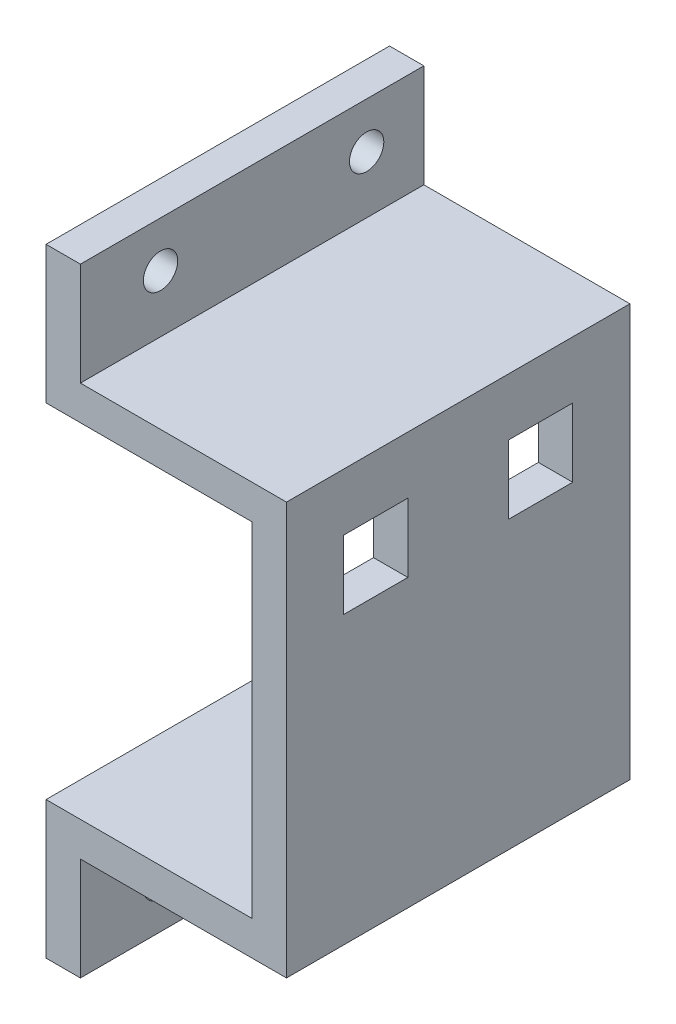
SolidWorks part; units mm, degrees
ref_plane "Front" through (0, 0, 0) normal (0, 0, 1) x (1, 0, 0)
ref_plane "Top" through (0, 0, 0) normal (0, 1, 0) x (1, 0, 0)
ref_plane "Right" through (0, 0, 0) normal (1, 0, 0) x (0, 0, -1)
sketch "草图1" plane through (0, 0, 0) normal (0, 0, 1) x (1, 0, 0)
  line L0 (0, 0) -> (18, 0)
  line L1 (18, 0) -> (18, -30)
  line L2 (18, -30) -> (0, -30)
  line L3 (0, -30) -> (0, -42)
  line L4 (0, 0) -> (0, 12)
  line L5 (3, 3) -> (3, 12)
  line L6 (3, 3) -> (21, 3)
  line L7 (21, 3) -> (21, -33)
  line L8 (21, -33) -> (3, -33)
  line L9 (3, -33) -> (3, -42)
  line L10 (0, 12) -> (3, 12)
  line L11 (3, -42) -> (0, -42)
  dimension "D1" = 12
  dimension "D2" = 30
  dimension "D3" = 18
  dimension "D4" = 3
extrude "凸台-拉伸1" add sketch "草图1" along normal mid plane 30
sketch "草图2" plane through (21, 0, 0) normal (1, 0, 0) x (0, 0, -1)
  line L0 (-15, -33) -> (-15, 3) construction
  line L1 (-10, -8) -> (-4.4, -8)
  line L2 (-10, -8) -> (-10, -2)
  line L3 (-10, -2) -> (-4.4, -2)
  line L4 (-4.4, -8) -> (-4.4, -2)
  line L5 (-10, -8) -> (-4.4, -2) construction
  line L6 (-10, -2) -> (-4.4, -8) construction
  line L7 (-15, 3) -> (15, 3) construction
  point P0 (-7.2, -5)
  dimension "D1" = 5.6
  dimension "D2" = 6
  dimension "D3" = 5
  dimension "D4" = 8
extrude "切除-拉伸1" cut sketch "草图2" against normal blind 20
mirror "镜向1" about plane through (0, 0, 0) normal (0, 0, 1) of "切除-拉伸1"
sketch "草图3" plane through (3, 0, 0) normal (1, 0, 0) x (0, 0, -1)
  line L1 (-8, 8) -> (10, 8) construction
  line L3 (-15, 3) -> (-15, 12) construction
  line L4 (-15, 12) -> (15, 12) construction
  circle A0 centre (10, 8) radius 1.5
  circle A1 centre (-8, 8) radius 1.5
  point P8 (0, 12)
  dimension "D2" = 3
  dimension "D1" = 18
  dimension "D3" = 7
  dimension "D4" = 4
extrude "切除-拉伸2" cut sketch "草图3" against normal blind 10 contours A1 | A0
ref_plane "基准面1" through (0, -15, 0) normal (0, -1, 0) x (-1, 0, 0)
mirror "镜向2" about plane through (0, -15, 0) normal (0, -1, 0) of "切除-拉伸2"
